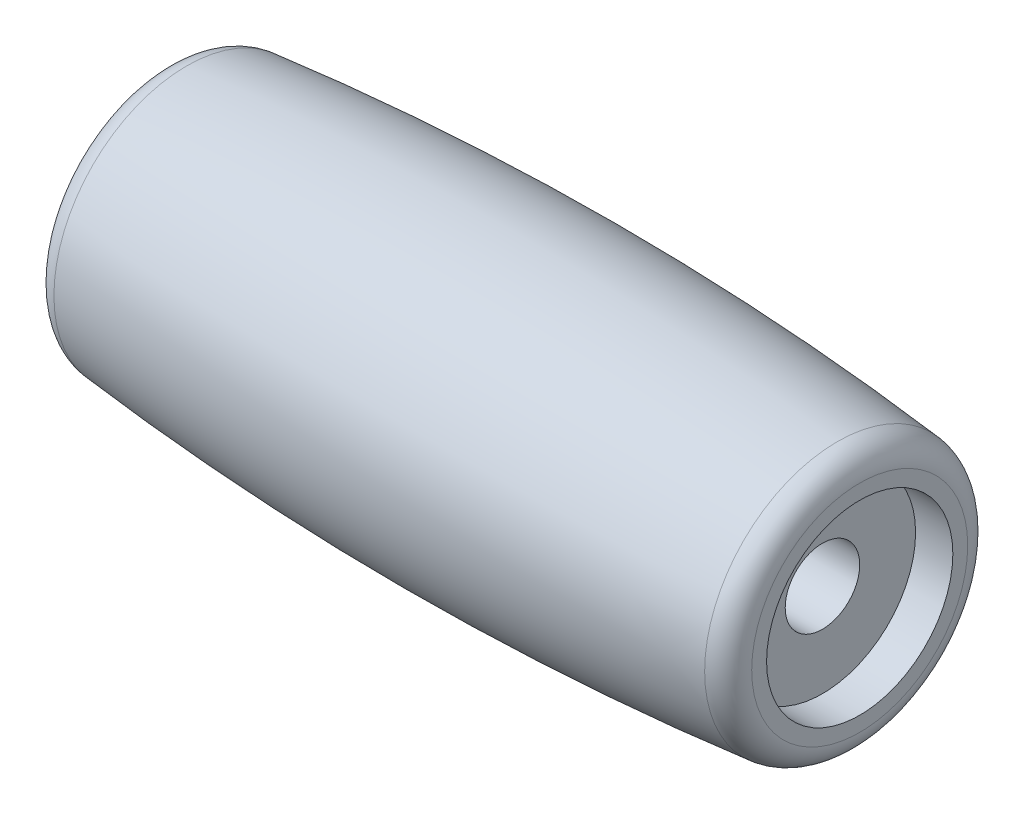
SolidWorks part; units mm, degrees
ref_plane "Front Plane" through (0, 0, 0) normal (0, 0, 1) x (1, 0, 0)
ref_plane "Top Plane" through (0, 0, 0) normal (0, 1, 0) x (1, 0, 0)
ref_plane "Right Plane" through (0, 0, 0) normal (1, 0, 0) x (0, 0, -1)
sketch "Sketch1" plane through (0, 0, 0) normal (0, 0, 1) x (1, 0, 0)
  line L0 (0, 12) -> (0, 0) construction
  line L1 (0, 0) -> (39.9041, 0) construction
  line L2 (-25, 3) -> (25, 3)
  line L3 (25, 3) -> (25, 7.5)
  line L4 (25, 7.5) -> (28, 7.5)
  line L5 (-25, 7.5) -> (-28, 7.5)
  line L6 (-25, 3) -> (-25, 7.5)
  line L7 (-28, 7.5) -> (-28, 8.6972)
  line L8 (28, 7.5) -> (28, 8.6972)
  arc A0 (-26.1999, 10.6871) -> (26.1999, 10.6871) centre (0, -250.0833) cw
  arc A1 (28, 8.6972) -> (26.1999, 10.6871) centre (26, 8.6972) ccw
  arc A2 (-28, 8.6972) -> (-26.1999, 10.6871) centre (-26, 8.6972) cw
  point P11 (0, 3)
  point P16 (28, 10.5)
  point P19 (-28, 10.5)
  dimension "D8" = 2
  dimension "D1" = 12
  dimension "D2" = 3
  dimension "D3" = 7.5
  dimension "D4" = 3
  dimension "D5" = 28
  dimension "D6" = 3
  dimension "D7" = 3
revolve "Revolve1" add sketch "Sketch1" angle 360 about L1
